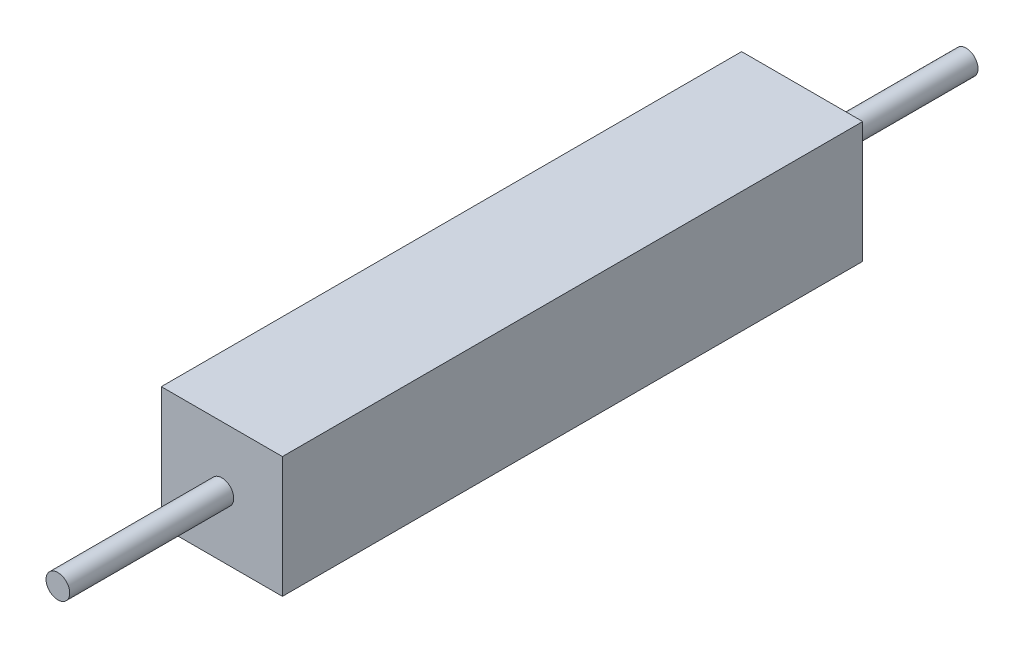
SolidWorks part; units mm, degrees
ref_plane "正面" through (0, 0, 0) normal (0, 0, 1) x (1, 0, 0)
ref_plane "平面" through (0, 0, 0) normal (0, 1, 0) x (1, 0, 0)
ref_plane "右側面" through (0, 0, 0) normal (1, 0, 0) x (0, 0, -1)
sketch "ｽｹｯﾁ1" plane through (0, 0, 0) normal (0, 0, 1) x (1, 0, 0)
  line L1 (0, 0) -> (2.4, 0)
  line L2 (0, 0) -> (0, 2.4)
  line L3 (0, 2.4) -> (2.4, 2.4)
  line L4 (2.4, 0) -> (2.4, 2.4)
  dimension "D1" = 2.4
  dimension "D2" = 2.4
extrude "ﾎﾞｽ - 押し出し1" add sketch "ｽｹｯﾁ1" along normal blind 11.5
sketch "ｽｹｯﾁ2" plane through (0, 0, 11.5) normal (0, 0, 1) x (1, 0, 0)
  line L0 (0, 1.2) -> (2.4, 1.2) construction
  line L1 (0, 2.4) -> (0, 0) construction
  line L2 (2.4, 0) -> (2.4, 2.4) construction
  line L3 (1.2, 2.4) -> (1.2, 0) construction
  line L4 (2.4, 2.4) -> (0, 2.4) construction
  line L5 (0, 0) -> (2.4, 0) construction
  circle A0 centre (1.2, 1.2) radius 0.235
  dimension "D1" = 0.47
extrude "ﾎﾞｽ - 押し出し2" add sketch "ｽｹｯﾁ2" along normal blind 3.25
sketch "ｽｹｯﾁ3" plane through (0, 0, 0) normal (0, 0, -1) x (-1, 0, 0)
  line L0 (-2.4, 1.2) -> (0, 1.2) construction
  line L1 (-2.4, 0) -> (-2.4, 2.4) construction
  line L2 (0, 2.4) -> (0, 0) construction
  line L3 (-1.2, 0) -> (-1.2, 2.4) construction
  line L4 (0, 0) -> (-2.4, 0) construction
  line L5 (-2.4, 2.4) -> (0, 2.4) construction
  circle A0 centre (-1.2, 1.2) radius 0.235
  dimension "D1" = 0.47
extrude "ﾎﾞｽ - 押し出し3" add sketch "ｽｹｯﾁ3" along normal blind 3.25
